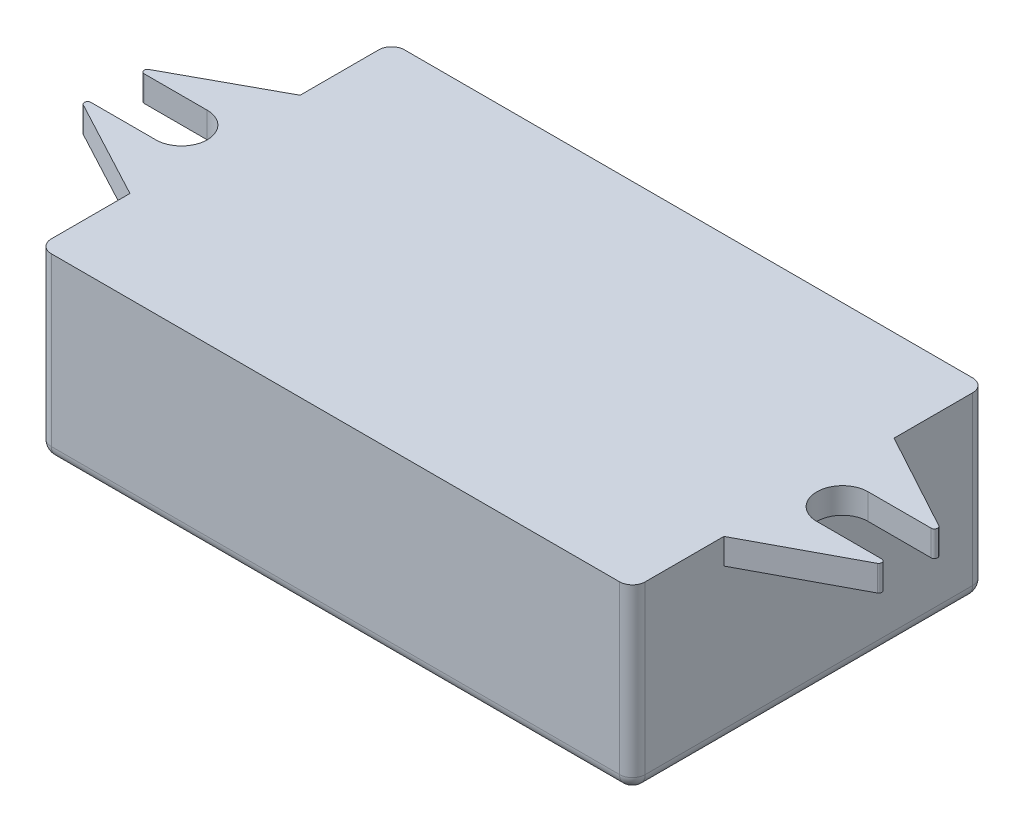
SolidWorks part; units mm, degrees
material "Custom Plastic"
ref_plane "Front Plane" through (0, 0, 0) normal (0, 0, 1) x (1, 0, 0)
ref_plane "Top Plane" through (0, 0, 0) normal (0, 1, 0) x (1, 0, 0)
ref_plane "Right Plane" through (0, 0, 0) normal (1, 0, 0) x (0, 0, -1)
sketch "Sketch1" plane through (0, 0, 0) normal (0, 1, 0) x (1, 0, 0)
  line L0 (33.0031, 5.8955) -> (41.5031, 1.2705)
  line L1 (-13.2469, 13.0205) -> (33.0031, 13.0205)
  line L3 (-13.2469, -14.4795) -> (33.0031, -14.4795)
  line L5 (41.5031, 1.2705) -> (35.6115, 1.2705)
  line L6 (35.6115, -2.7295) -> (41.6726, -2.7295)
  line L7 (41.6726, -2.7295) -> (33.0031, -7.3545)
  line L8 (9.8781, 13.0205) -> (9.8781, -14.4795) construction
  line L9 (-21.9163, -2.7295) -> (-13.2469, -7.3545)
  line L10 (-15.8553, -2.7295) -> (-21.9163, -2.7295)
  line L11 (-21.7469, 1.2705) -> (-15.8553, 1.2705)
  line L12 (-13.2469, 5.8955) -> (-21.7469, 1.2705)
  line L15 (-13.2469, 5.8955) -> (-13.2469, 13.0205)
  line L16 (33.0031, 13.0205) -> (33.0031, 5.8955)
  line L17 (33.0031, -7.3545) -> (33.0031, -14.4795)
  line L18 (-13.2469, -14.4795) -> (-13.2469, -7.3545)
  arc A0 (35.6115, 1.2705) -> (35.6115, -2.7295) centre (35.6115, -0.7295) ccw
  arc A1 (-15.8553, 1.2705) -> (-15.8553, -2.7295) centre (-15.8553, -0.7295) cw
  dimension "D1" = 27.5
  dimension "D2" = 46.25
  dimension "D3" = 7.125
  dimension "D4" = 7.125
  dimension "D5" = 8.5
  dimension "D6" = 4
  dimension "D7" = 4.625
  dimension "D8" = 8.6694
extrude "Boss-Extrude3" add sketch "Sketch1" along normal blind 2 contours L1 L16 L0 L5 A0 L6 L7 L17 L3 L18 L9 L10 A1 L11 L12 L15
sketch "Sketch4" plane through (0, 0, 0) normal (0, -1, 0) x (1, 0, 0)
  line L1 (-13.2469, 14.4795) -> (33.0031, 14.4795)
  line L2 (-13.2469, 14.4795) -> (-13.2469, -13.0205)
  line L3 (-13.2469, -13.0205) -> (33.0031, -13.0205)
  line L4 (33.0031, 14.4795) -> (33.0031, -13.0205)
extrude "Boss-Extrude4" add sketch "Sketch4" along normal blind 12
fillet "Fillet1" radius 1 1 edges at (9.8781, -12, 14.4795)
fillet "Fillet2" radius 1 9 edges at (33.0031, -11.7071, 14.1866) (-13.2469, -11.7071, 14.1866) (-13.2469, -4.5, 14.4795) (33.0031, -4.5, 14.4795) (-13.2469, -5, -13.0205) (33.0031, -5, -13.0205) (33.0031, -12, 0.2295) (9.8781, -12, -13.0205) (-13.2469, -12, 0.2295)
fillet "Fillet3" radius 0.25 4 edges at (41.5031, 1, -1.2705) (41.6726, 1, 2.7295) (-21.7469, 1, -1.2705) (-21.9163, 1, 2.7295)
